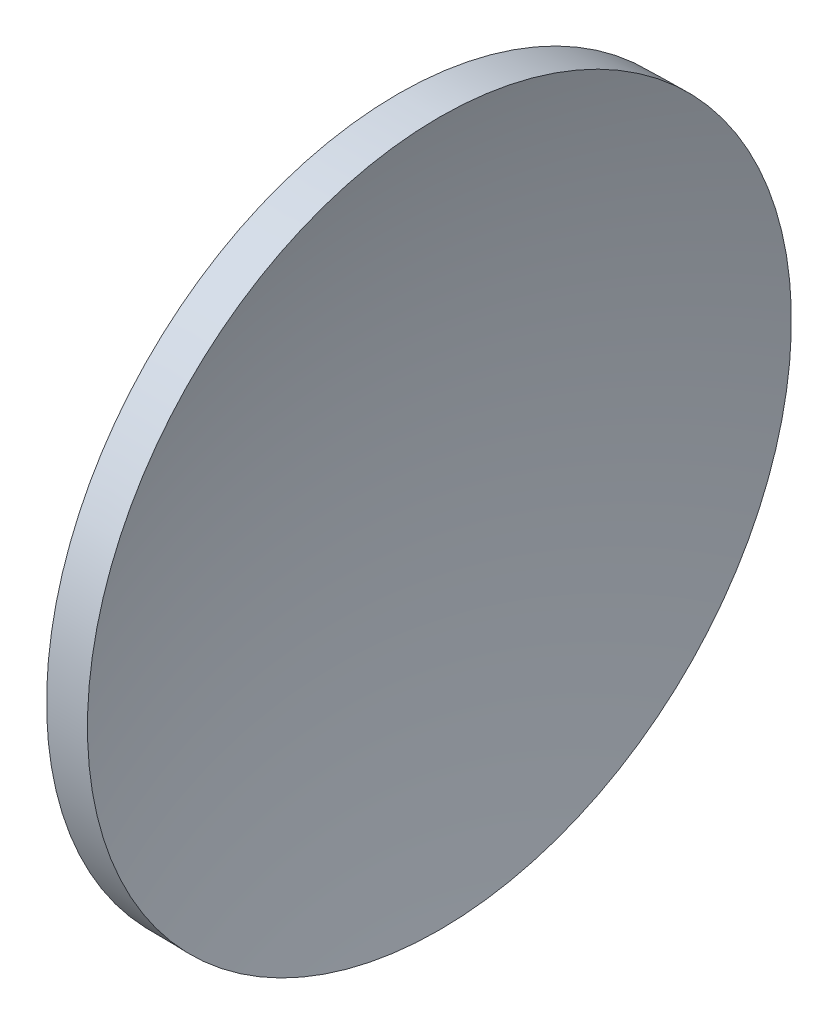
SolidWorks part; units mm, degrees
ref_plane "前视基准面" through (0, 0, 0) normal (0, 0, 1) x (1, 0, 0)
ref_plane "上视基准面" through (0, 0, 0) normal (0, 1, 0) x (1, 0, 0)
ref_plane "右视基准面" through (0, 0, 0) normal (1, 0, 0) x (0, 0, -1)
sketch "草图1" plane through (0, 0, 0) normal (0, 0, 1) x (1, 0, 0)
  line L0 (115.9445, 65.2168) -> (135.9482, 65.2168) construction
  line L1 (125.4806, 77.7228) -> (126.9556, 77.7439)
  line L2 (125.0675, 65.2168) -> (122.5675, 65.2168)
  arc A0 (125.4806, 77.7228) -> (122.5675, 65.2168) centre (150.8675, 65.2168) ccw
  arc A1 (126.9556, 77.7439) -> (125.0675, 65.2168) centre (167.5675, 65.2168) ccw
  dimension "D1" = 42.5
  dimension "D2" = 28.3
revolve "旋转1" add sketch "草图1" angle 360 about L0
